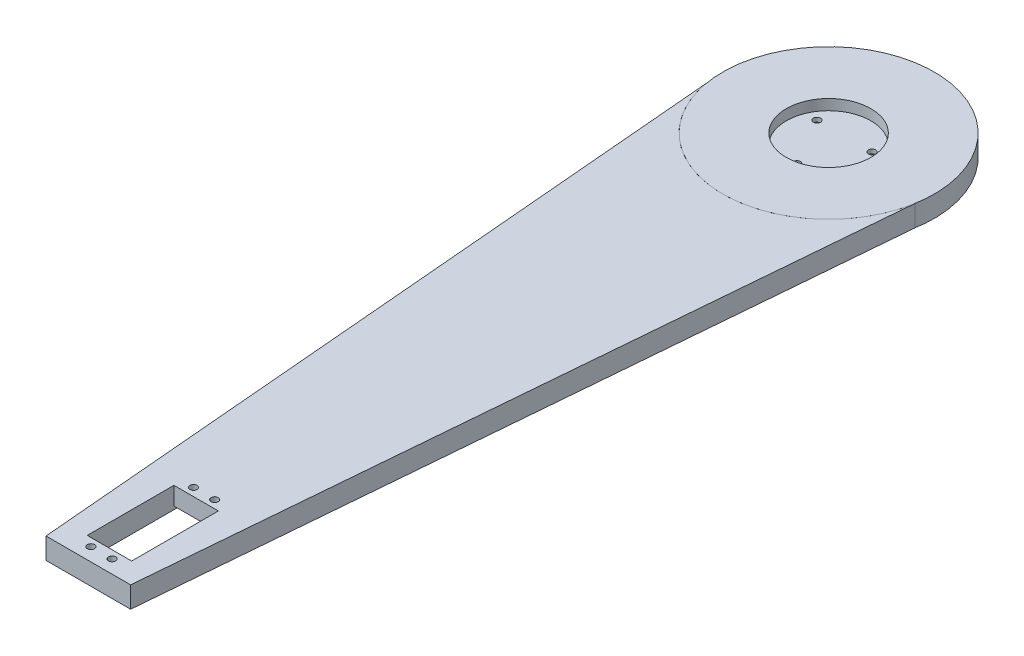
SolidWorks part; units mm, degrees
ref_plane "Front Plane" through (0, 0, 0) normal (0, 0, 1) x (1, 0, 0)
ref_plane "Top Plane" through (0, 0, 0) normal (0, 1, 0) x (1, 0, 0)
ref_plane "Right Plane" through (0, 0, 0) normal (1, 0, 0) x (0, 0, -1)
sketch "Sketch1" plane through (0, 0, 0) normal (0, 1, 0) x (1, 0, 0)
  circle A0 centre (0, 0) radius 50
extrude "Boss-Extrude1" add sketch "Sketch1" along normal blind 10
sketch "Sketch2" plane through (0, 10, 0) normal (0, 1, 0) x (1, 0, 0)
  circle A0 centre (0, 0) radius 20
extrude "Cut-Extrude1" cut sketch "Sketch2" against normal blind 5
sketch "Sketch7" plane through (0, 0, 0) normal (0, -1, 0) x (1, 0, 0)
  line L0 (10.1404, -5.8546) -> (10.1404, -9.1454)
  line L1 (0, 11.7091) -> (2.85, 13.3546)
  line L2 (2.85, 13.3546) -> (2.85, 16.6454)
  line L3 (2.85, 16.6454) -> (0, 18.2909)
  line L4 (0, 18.2909) -> (-2.85, 16.6454)
  line L5 (-2.85, 16.6454) -> (-2.85, 13.3546)
  line L6 (-2.85, 13.3546) -> (0, 11.7091)
  line L7 (10.1404, -9.1454) -> (12.9904, -10.7909)
  line L8 (12.9904, -10.7909) -> (15.8404, -9.1454)
  line L9 (15.8404, -9.1454) -> (15.8404, -5.8546)
  line L10 (15.8404, -5.8546) -> (12.9904, -4.2091)
  line L11 (12.9904, -4.2091) -> (10.1404, -5.8546)
  line L12 (-10.1404, -5.8546) -> (-12.9904, -4.2091)
  line L13 (-12.9904, -4.2091) -> (-15.8404, -5.8546)
  line L14 (-15.8404, -5.8546) -> (-15.8404, -9.1454)
  line L15 (-15.8404, -9.1454) -> (-12.9904, -10.7909)
  line L16 (-12.9904, -10.7909) -> (-10.1404, -9.1454)
  line L17 (-10.1404, -9.1454) -> (-10.1404, -5.8546)
  circle A0 centre (0, 0) radius 15
  circle A1 centre (0, 15) radius 2.85 construction
  point P25 (0, 0)
  dimension "D1" = 3
extrude "Cut-Extrude6" cut sketch "Sketch7" against normal blind 3 contours A0 L2 L3 L4 L5 | L2 A0 L5 L6 L1 | L13 L14 L15 L16 L17 L12 | L10 L11 L0 L7 L8 L9
sketch "Sketch8" plane through (0, 0, 0) normal (0, -1, 0) x (1, 0, 0)
  line L0 (-2.85, 15) -> (2.85, 15) construction
  line L1 (-2.85, 16.6454) -> (-2.85, 13.3546) construction
  line L2 (2.85, 13.3546) -> (2.85, 16.6454) construction
  circle A0 centre (0, 15) radius 1.7
  circle A1 centre (12.9904, -7.5) radius 1.7
  circle A2 centre (-12.9904, -7.5) radius 1.7
  point P14 (0, 0)
  dimension "D1" = 3
extrude "Cut-Extrude7" cut sketch "Sketch8" against normal blind 10
sketch "Sketch9" plane through (0, 0, 0) normal (0, -1, 0) x (1, 0, 0)
  line L1 (-50, 0) -> (50, 0)
  line L2 (-50, 0) -> (-50, 350)
  line L3 (-50, 350) -> (50, 350)
  line L4 (50, 0) -> (50, 350)
  circle A0 centre (0, 0) radius 50 construction
  circle A1 centre (0, 0) radius 50
  circle M23 centre (0, 0) radius 50
  dimension "D1" = 350
extrude "Boss-Extrude3" add sketch "Sketch9" against normal blind 10 separate body contours L4 L3 L2 M23
sketch "Sketch10" plane through (0, 0, 0) normal (0, -1, 0) x (1, 0, 0)
  line L0 (0, 350) -> (0, 0) construction
  line L1 (-50, 350) -> (50, 350) construction
  line L3 (-10.5, 299) -> (10.5, 299)
  line L4 (-10.5, 299) -> (-10.5, 340)
  line L5 (-10.5, 340) -> (10.5, 340)
  line L6 (10.5, 299) -> (10.5, 340)
  line L7 (-10.5, 299) -> (10.5, 340) construction
  line L8 (-10.5, 340) -> (10.5, 299) construction
  point P5 (0, 319.5)
  dimension "D1" = 41
  dimension "D2" = 21
  dimension "D3" = 10
extrude "Cut-Extrude8" cut sketch "Sketch10" against normal blind 10
sketch "Sketch11" plane through (0, 0, 0) normal (0, -1, 0) x (1, 0, 0)
  line L0 (-10.5, 340) -> (-10.5, 299) construction
  line L1 (-10.5, 292.5) -> (10.5, 292.5)
  line L2 (-10.5, 292.5) -> (-10.5, 346.5)
  line L3 (-10.5, 346.5) -> (10.5, 346.5)
  line L4 (10.5, 292.5) -> (10.5, 346.5)
  line L5 (-10.5, 292.5) -> (10.5, 346.5) construction
  line L6 (-10.5, 346.5) -> (10.5, 292.5) construction
  line L7 (-10.5, 340) -> (-10.5, 299)
  line L8 (10.5, 340) -> (-10.5, 340) construction
  line L9 (10.5, 340) -> (-10.5, 340)
  point P0 (0, 319.5)
  point P5 (0, 0)
  point P8 (-10.5, 319.5)
  point P9 (-10.5, 319.5)
  point P11 (0, 346.5)
  point P12 (0, 340)
  line M6 (10.5, 299) -> (-10.5, 299)
  line M8 (-10.5, 340) -> (10.5, 340)
  dimension "D1" = 54
  dimension "D2" = 21
extrude "Cut-Extrude9" cut sketch "Sketch11" against normal blind 1.5 contours L4 L3 L2 M8 | L1 L4 L2 M6
sketch "Sketch12" plane through (0, 1.5, 0) normal (0, -1, 0) x (1, 0, 0)
  line L0 (-5, 343.75) -> (5, 343.75) construction
  line L1 (-10.5, 340) -> (10.5, 340) construction
  line L2 (-10.5, 346.5) -> (10.5, 346.5) construction
  line L3 (-10.5, 346.5) -> (10.5, 346.5)
  line L4 (-10.5, 319.5) -> (10.5, 319.5) construction
  line L5 (-10.5, 346.5) -> (-10.5, 292.5) construction
  line L6 (10.5, 292.5) -> (10.5, 346.5) construction
  circle A0 centre (-5, 343.75) radius 1.7
  circle A1 centre (5, 343.75) radius 1.7
  circle A2 centre (-5, 295.25) radius 1.7
  circle A3 centre (5, 295.25) radius 1.7
  point P3 (0, 343.75)
  point P9 (0, 346.5)
  dimension "D1" = 3.75
extrude "Cut-Extrude10" cut sketch "Sketch12" against normal blind 9 contours A0 | A1 | A2 | A3
sketch "Sketch13" plane through (0, 0, 0) normal (0, -1, 0) x (1, 0, 0)
  line L0 (-50, 0) -> (-20, 350)
  line L1 (0, 350) -> (0, 0) construction
  line L2 (50, 0) -> (20, 350)
  line L3 (50, 0) -> (50, 350)
  line L4 (50, 350) -> (-50, 350)
  line L5 (-50, 350) -> (-50, 0)
  line L6 (50, 0) -> (50, 350)
  line L7 (50, 350) -> (-50, 350)
  line L8 (-50, 350) -> (-50, 0)
  arc A1 (50, 0) -> (-50, 0) centre (0, 0) ccw
  arc A2 (50, 0) -> (-50, 0) centre (0, 0) ccw
  arc M7 (-50, 0) -> (50, 0) centre (0, 0) cw
  line M8 (50, 0) -> (50, 350)
  line M9 (50, 350) -> (-50, 350)
  line M10 (-50, 350) -> (-50, 0)
  dimension "D2" = 20
  dimension "D1" = 0
extrude "Cut-Extrude11" cut sketch "Sketch13" against normal blind 10 contours L0 M7 M9 M10 | L2 M7 M8 M9
